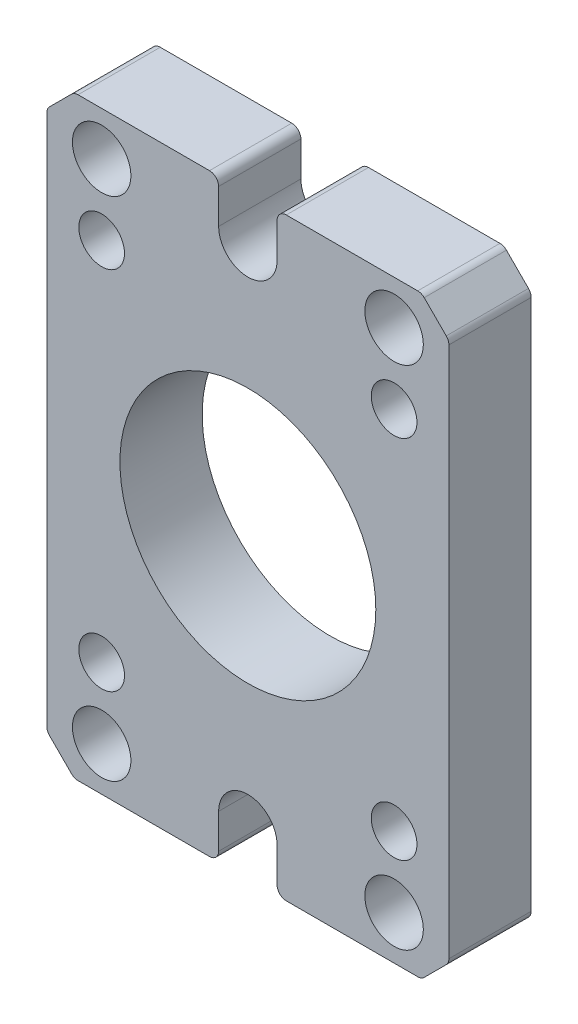
SolidWorks part; units mm, degrees
ref_plane "Plano frontal" through (0, 0, 0) normal (0, 0, 1) x (1, 0, 0)
ref_plane "Plano superior" through (0, 0, 0) normal (0, 1, 0) x (1, 0, 0)
ref_plane "Plano direito" through (0, 0, 0) normal (1, 0, 0) x (0, 0, -1)
ref_plane "Plano1" through (0, 0, 0) normal (0, 0, -1) x (-1, 0, 0)
sketch "Esboço1" plane through (0, 0, 0) normal (0, 0, -1) x (-1, 0, 0)
  line L0 (-2.1, 16.25) -> (-9.2929, 16.25)
  line L1 (-9.6464, 16.1036) -> (-10.8536, 14.8964)
  line L2 (-11, 14.5429) -> (-11, -14.5429)
  line L3 (-10.8536, -14.8964) -> (-9.6464, -16.1036)
  line L4 (-9.2929, -16.25) -> (-2.1, -16.25)
  line L5 (-1.6, -15.75) -> (-1.6, -13.8564)
  line L6 (1.6, -13.8564) -> (1.6, -15.75)
  line L7 (2.1, -16.25) -> (9.2929, -16.25)
  line L8 (9.6464, -16.1036) -> (10.8536, -14.8964)
  line L9 (11, -14.5429) -> (11, 14.5429)
  line L10 (10.8536, 14.8964) -> (9.6464, 16.1036)
  line L11 (9.2929, 16.25) -> (2.1, 16.25)
  line L12 (1.6, 15.75) -> (1.6, 13.8564)
  line L13 (-1.6, 13.8564) -> (-1.6, 15.75)
  circle A0 centre (0, 0) radius 7
  circle A1 centre (-8, -13.8564) radius 1.6
  circle A2 centre (8, -13.8564) radius 1.6
  circle A3 centre (8, 13.8564) radius 1.6
  circle A4 centre (-8, 13.8564) radius 1.6
  circle A5 centre (-8, -10) radius 1.25
  circle A6 centre (8, -10) radius 1.25
  circle A7 centre (8, 10) radius 1.25
  circle A8 centre (-8, 10) radius 1.25
  arc A9 (-9.2929, 16.25) -> (-9.6464, 16.1036) centre (-9.2929, 15.75) ccw
  arc A10 (-10.8536, 14.8964) -> (-11, 14.5429) centre (-10.5, 14.5429) ccw
  arc A11 (-11, -14.5429) -> (-10.8536, -14.8964) centre (-10.5, -14.5429) ccw
  arc A12 (-9.6464, -16.1036) -> (-9.2929, -16.25) centre (-9.2929, -15.75) ccw
  arc A13 (-2.1, -16.25) -> (-1.6, -15.75) centre (-2.1, -15.75) ccw
  arc A14 (-1.6, -13.8564) -> (1.6, -13.8564) centre (0, -13.8564) cw
  arc A15 (1.6, -15.75) -> (2.1, -16.25) centre (2.1, -15.75) ccw
  arc A16 (9.2929, -16.25) -> (9.6464, -16.1036) centre (9.2929, -15.75) ccw
  arc A17 (10.8536, -14.8964) -> (11, -14.5429) centre (10.5, -14.5429) ccw
  arc A18 (11, 14.5429) -> (10.8536, 14.8964) centre (10.5, 14.5429) ccw
  arc A19 (9.6464, 16.1036) -> (9.2929, 16.25) centre (9.2929, 15.75) ccw
  arc A20 (2.1, 16.25) -> (1.6, 15.75) centre (2.1, 15.75) ccw
  arc A21 (1.6, 13.8564) -> (-1.6, 13.8564) centre (0, 13.8564) cw
  arc A22 (-1.6, 15.75) -> (-2.1, 16.25) centre (-2.1, 15.75) ccw
extrude "Ressalto-extrusão1" add sketch "Esboço1" against normal blind 4.5
